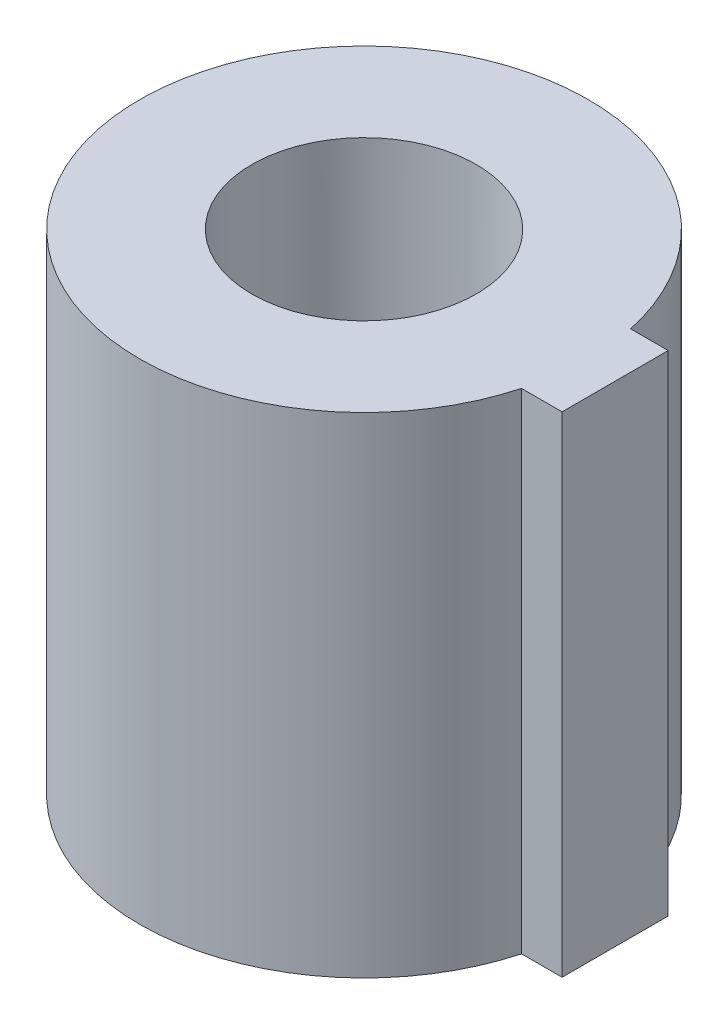
SolidWorks part; units mm, degrees
ref_plane "Front Plane" through (0, 0, 0) normal (0, 0, 1) x (1, 0, 0)
ref_plane "Top Plane" through (0, 0, 0) normal (0, 1, 0) x (1, 0, 0)
ref_plane "Right Plane" through (0, 0, 0) normal (1, 0, 0) x (0, 0, -1)
sketch "Sketch1" plane through (0, 0, 0) normal (0, 1, 0) x (1, 0, 0)
  circle A0 centre (0, 0) radius 5.5
  dimension "D1" = 11
extrude "Boss-Extrude1" add sketch "Sketch1" along normal blind 12
sketch "Sketch2" plane through (0, 12, 0) normal (0, 1, 0) x (1, 0, 0)
  line L1 (6.3, 1.1527) -> (3.3, 1.1527)
  line L2 (6.3, 1.1527) -> (6.3, -1.4473)
  line L3 (6.3, -1.4473) -> (3.3, -1.4473)
  line L4 (3.3, 1.1527) -> (3.3, -1.4473)
  line L5 (6.3, 1.1527) -> (3.3, -1.4473) construction
  line L6 (6.3, -1.4473) -> (3.3, 1.1527) construction
  circle A0 centre (0, 0) radius 5.5 construction
  point P0 (4.8, -0.1473)
  dimension "D1" = 2.6
  dimension "D2" = 4.8
  dimension "D3" = 3
extrude "Boss-Extrude2" add sketch "Sketch2" against normal blind 12
sketch "Sketch3" plane through (0, 0, 0) normal (0, -1, 0) x (-1, 0, 0)
  line L1 (-1.8916, 4.0868) -> (-4.4851, 0.4052)
  line L2 (-4.4851, 0.4052) -> (-2.5935, -3.6816)
  line L3 (-2.5935, -3.6816) -> (1.8916, -4.0868)
  line L4 (1.8916, -4.0868) -> (4.4851, -0.4052)
  line L5 (4.4851, -0.4052) -> (2.5935, 3.6816)
  line L6 (2.5935, 3.6816) -> (-1.8916, 4.0868)
  circle A0 centre (0, 0) radius 3.9 construction
  dimension "D1" = 7.8
extrude "Cut-Extrude1" cut sketch "Sketch3" against normal blind 3.8
sketch "Sketch5" plane through (0, 12, 0) normal (0, 1, 0) x (1, 0, 0)
  circle A0 centre (0, 0) radius 2.75
  dimension "D1" = 5.5
extrude "Cut-Extrude3" cut sketch "Sketch5" against normal blind 17.65
